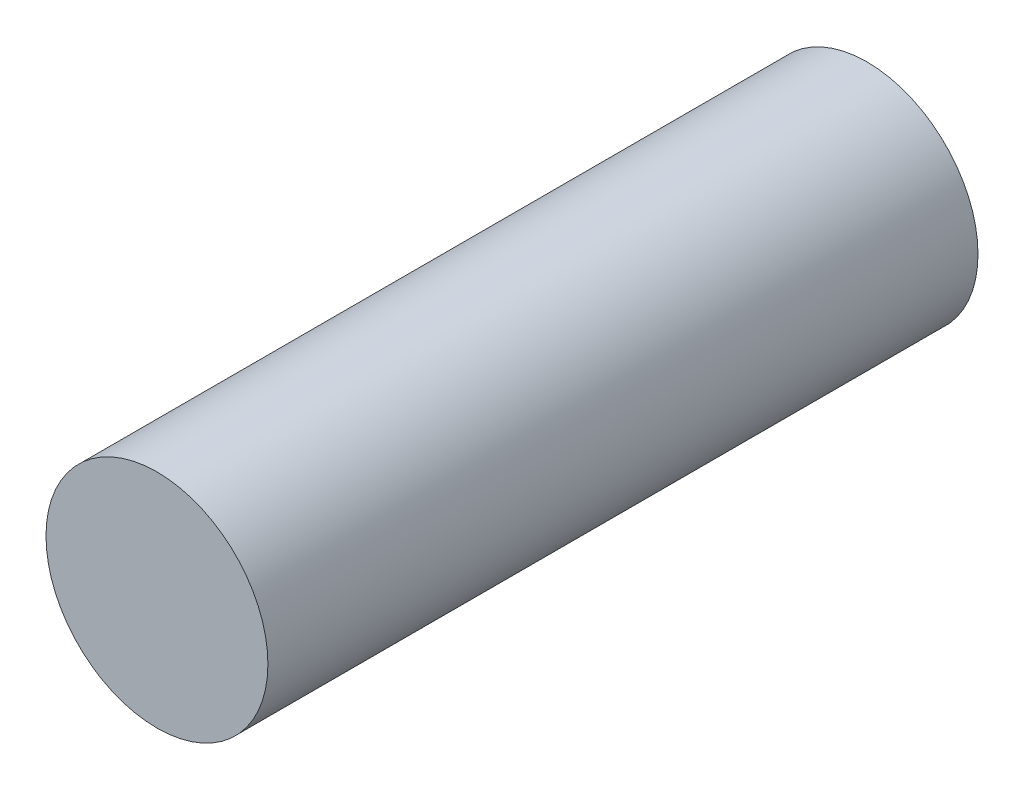
SolidWorks part; units mm, degrees
ref_plane "Front" through (0, 0, 0) normal (0, 0, 1) x (1, 0, 0)
ref_plane "Top" through (0, 0, 0) normal (0, 1, 0) x (1, 0, 0)
ref_plane "Right" through (0, 0, 0) normal (1, 0, 0) x (0, 0, -1)
sketch "Sketch1" plane through (0, 0, 0) normal (0, 0, 1) x (1, 0, 0)
  circle A0 centre (0, 0) radius 6.25
  dimension "D1" = 12.5
extrude "Boss-Extrude1" add sketch "Sketch1" along normal blind 40
